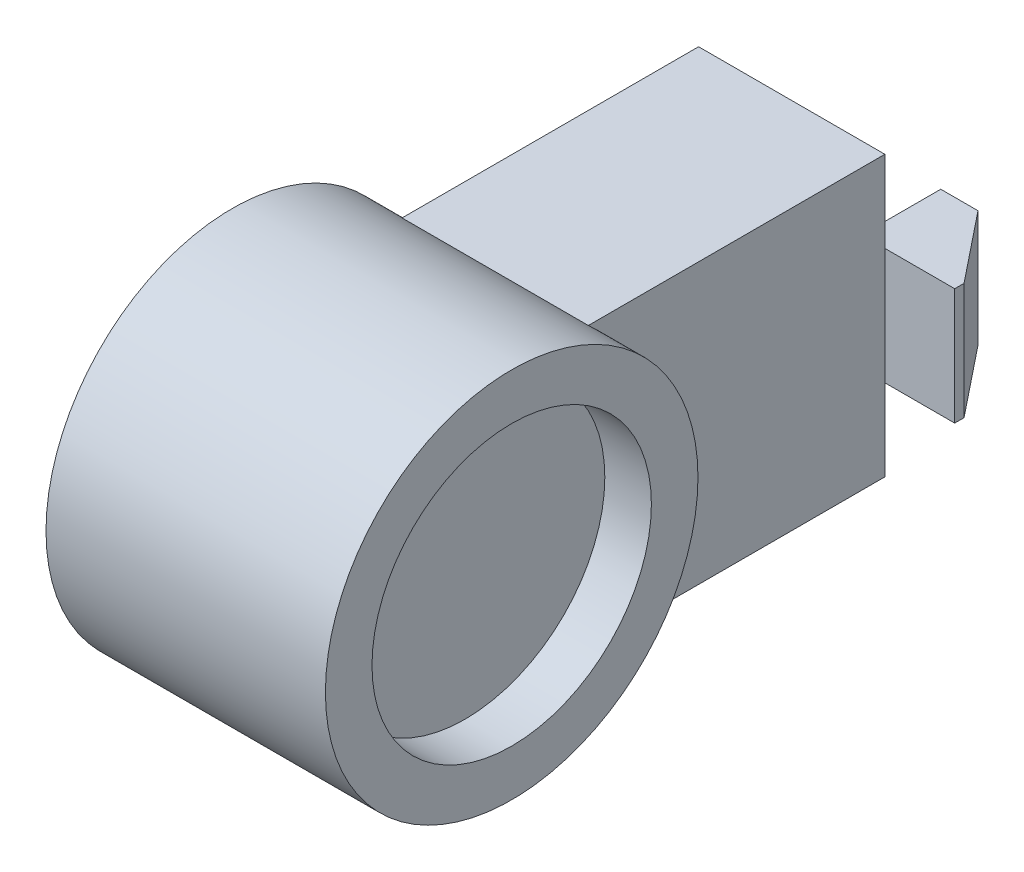
SolidWorks part; units mm, degrees
ref_plane "Front Plane" through (0, 0, 0) normal (0, 0, 1) x (1, 0, 0)
ref_plane "Top Plane" through (0, 0, 0) normal (0, 1, 0) x (1, 0, 0)
ref_plane "Right Plane" through (0, 0, 0) normal (1, 0, 0) x (0, 0, -1)
sketch "Sketch1" plane through (0, 0, 0) normal (1, 0, 0) x (0, 0, -1)
  circle A0 centre (0, 0) radius 40
  dimension "D1" = 80
extrude "Boss-Extrude1" add sketch "Sketch1" along normal blind 60
sketch3d "3DSketch1"
  point P0 (29.3748, -3.2568, 39.8672)
ref_plane "Plane1" through (0, 0, -90.1328) normal (0, 0, 1) x (1, 0, 0)
sketch "Sketch2" plane through (0, 0, -90.1328) normal (0, 0, 1) x (1, 0, 0)
  line L0 (60, 0) -> (30, 0) construction
  line L1 (60, -40) -> (60, 40) construction
  line L3 (10, 30) -> (50, 30)
  line L4 (10, 30) -> (10, -30)
  line L5 (10, -30) -> (50, -30)
  line L6 (50, 30) -> (50, -30)
  line L7 (10, 30) -> (50, -30) construction
  line L8 (10, -30) -> (50, 30) construction
  dimension "D1" = 30
  dimension "D2" = 40
  dimension "D3" = 60
extrude "Boss-Extrude3" add sketch "Sketch2" along normal up to surface (63.6753 mm away)
sketch "Sketch3" plane through (0, 0, -90.1328) normal (0, 0, -1) x (-1, 0, 0)
  line L0 (-10, 0) -> (-30, 0) construction
  line L1 (-10, -30) -> (-10, 30) construction
  line L2 (-30, -30) -> (-30, 0) construction
  line L3 (-65, 12.5) -> (5, 12.5)
  line L4 (-65, 12.5) -> (-65, -12.5)
  line L5 (-65, -12.5) -> (5, -12.5)
  line L6 (5, 12.5) -> (5, -12.5)
  line L7 (-65, 12.5) -> (5, -12.5) construction
  line L8 (-65, -12.5) -> (5, 12.5) construction
  line L10 (-10, -30) -> (-50, -30) construction
  dimension "D1" = 20
  dimension "D2" = 70
  dimension "D3" = 25
  dimension "D4" = 30
extrude "Boss-Extrude4" add sketch "Sketch3" along normal blind 2
sketch "Sketch5" plane through (0, 12.5, 0) normal (0, 1, 0) x (1, 0, 0)
  line L0 (-5, 92.1328) -> (7, 107.1328)
  line L1 (7, 107.1328) -> (15, 107.1328)
  line L2 (15, 107.1328) -> (15, 92.1328)
  line L3 (-5, 92.1328) -> (65, 92.1328) construction
  line L4 (15, 92.1328) -> (-5, 92.1328)
  line L5 (30, 92.1328) -> (30, 111.7053) construction
  line L6 (45, 107.1328) -> (45, 92.1328)
  line L7 (53, 107.1328) -> (45, 107.1328)
  line L8 (65, 92.1328) -> (53, 107.1328)
  line L9 (45, 92.1328) -> (65, 92.1328)
  dimension "D1" = 15
  dimension "D2" = 8
  dimension "D3" = 20
extrude "Boss-Extrude5" add sketch "Sketch5" against normal blind 25
sketch "Sketch8" plane through (60, 0, 0) normal (1, 0, 0) x (0, 0, -1)
  circle A0 centre (0, 0) radius 30
  dimension "D1" = 60
extrude "Cut-Extrude3" cut sketch "Sketch8" against normal blind 10
sketch "Sketch9" plane through (0, 0, 0) normal (-1, 0, 0) x (0, 0, 1)
  circle A0 centre (0, 0) radius 6
  dimension "D1" = 12
extrude "Cut-Extrude4" cut sketch "Sketch9" against normal blind 6
